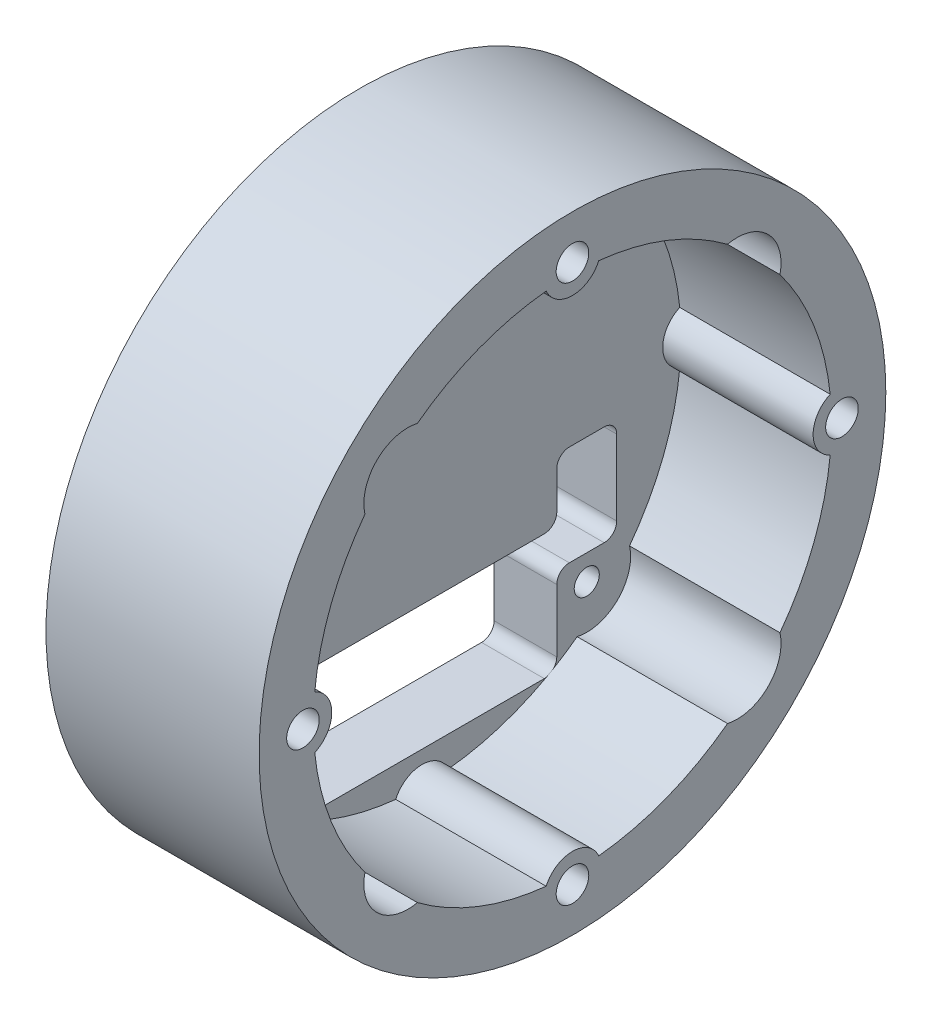
SolidWorks part; units mm, degrees
ref_plane "Front Plane" through (0, 0, 0) normal (0, 0, 1) x (1, 0, 0)
ref_plane "Top Plane" through (0, 0, 0) normal (0, 1, 0) x (1, 0, 0)
ref_plane "Right Plane" through (0, 0, 0) normal (1, 0, 0) x (0, 0, -1)
sketch "Sketch1" plane through (0, 0, 0) normal (1, 0, 0) x (0, 0, -1)
  circle A0 centre (0, 0) radius 25
  dimension "D1" = 50
extrude "Boss-Extrude1" add sketch "Sketch1" along normal blind 5
sketch "Sketch3" plane through (0, 0, 0) normal (-1, 0, 0) x (0, 0, 1)
  circle A0 centre (-13.14, 13.14) radius 1
  circle A1 centre (13.14, 13.14) radius 1
  circle A2 centre (13.14, -13.14) radius 1
  circle A3 centre (-13.14, -13.14) radius 1
  point P12 (0, 0)
  dimension "D1" = 2
  dimension "D2" = 13.14
  dimension "D3" = 13.14
  dimension "D4" = 4
extrude "Cut-Extrude2" cut sketch "Sketch3" against normal through all
sketch "Sketch4" plane through (5, 0, 0) normal (1, 0, 0) x (0, 0, -1)
  circle A0 centre (0, 0) radius 25
  circle A1 centre (0, 0) radius 20.6667
  dimension "D1" = 50
  dimension "D2" = 41.3333
extrude "Boss-Extrude2" add sketch "Sketch4" along normal blind 12
sketch "Sketch2" plane through (5, 0, 0) normal (1, 0, 0) x (0, 0, -1)
  line L0 (0, 21.5) -> (0, 25) construction
  circle A1 centre (0, 21.5) radius 1.3
  circle A3 centre (0, 0) radius 25 construction
  circle A8 centre (21.5, 0) radius 1.3
  circle A9 centre (0, -21.5) radius 1.3
  circle A10 centre (-21.5, 0) radius 1.3
  point P16 (0, 0)
  dimension "D2" = 2.6
  dimension "D1" = 21.5
  dimension "D3" = 4
extrude "Cut-Extrude1" cut sketch "Sketch2" against normal through all both and the other way through all
sketch "Sketch5" plane through (5, 0, 0) normal (1, 0, 0) x (0, 0, -1)
  line L0 (-13.14, -13.14) -> (13.14, -13.14) construction
  line L1 (9.75, -8.14) -> (-9.75, -8.14)
  line L2 (10.75, -12.14) -> (10.75, -17.14)
  line L3 (9.75, -18.14) -> (-9.75, -18.14)
  line L4 (-10.75, -9.14) -> (-10.75, -17.14)
  line L5 (10.75, -8.14) -> (-10.75, -18.14) construction
  line L6 (10.75, -18.14) -> (-10.75, -8.14) construction
  line L8 (14.53, -3.14) -> (11.75, -3.14)
  line L9 (15.53, -4.14) -> (15.53, -10.14)
  line L10 (14.53, -11.14) -> (11.75, -11.14)
  line L11 (10.75, -4.14) -> (10.75, -7.14)
  line L12 (15.53, -3.14) -> (10.75, -11.14) construction
  line L13 (15.53, -11.14) -> (10.75, -3.14) construction
  arc A0 (11.75, -11.14) -> (10.75, -12.14) centre (11.75, -12.14) ccw
  arc A1 (-10.75, -9.14) -> (-9.75, -8.14) centre (-9.75, -9.14) cw
  arc A2 (-9.75, -18.14) -> (-10.75, -17.14) centre (-9.75, -17.14) cw
  arc A3 (10.75, -17.14) -> (9.75, -18.14) centre (9.75, -17.14) cw
  arc A4 (15.53, -10.14) -> (14.53, -11.14) centre (14.53, -10.14) cw
  arc A5 (10.75, -4.14) -> (11.75, -3.14) centre (11.75, -4.14) cw
  arc A6 (15.53, -4.14) -> (14.53, -3.14) centre (14.53, -4.14) ccw
  arc A7 (9.75, -8.14) -> (10.75, -7.14) centre (9.75, -7.14) ccw
  point P0 (0, -13.14)
  point P5 (13.14, -7.14)
  dimension "D5" = 1
  dimension "D6" = 1
  dimension "D1" = 10
  dimension "D2" = 21.5
  dimension "D3" = 8
  dimension "D4" = 2
extrude "Cut-Extrude3" cut sketch "Sketch5" against normal through all
sketch "Sketch7" plane through (5, 0, 0) normal (1, 0, 0) x (0, 0, -1)
  line L0 (-13.14, 13.14) -> (13.14, -13.14) construction
  line L1 (-10.6651, 15.6149) -> (0, 4.9497)
  line L2 (-15.6149, 10.6651) -> (-4.9497, 0)
  line L3 (13.14, 13.14) -> (-13.14, -13.14) construction
  line L4 (15.6149, 10.6651) -> (4.9497, 0)
  line L5 (10.6651, 15.6149) -> (0, 4.9497)
  line L6 (0, -4.9497) -> (10.6651, -15.6149)
  line L7 (0, -4.9497) -> (-10.6651, -15.6149)
  line L8 (4.9497, 0) -> (15.6149, -10.6651)
  line L9 (-4.9497, 0) -> (-15.6149, -10.6651)
  arc A0 (-10.6651, 15.6149) -> (-15.6149, 10.6651) centre (-13.14, 13.14) ccw
  arc A1 (10.6651, -15.6149) -> (15.6149, -10.6651) centre (13.14, -13.14) ccw
  arc A2 (15.6149, 10.6651) -> (10.6651, 15.6149) centre (13.14, 13.14) ccw
  arc A3 (-15.6149, -10.6651) -> (-10.6651, -15.6149) centre (-13.14, -13.14) ccw
  point P2 (0, 0)
  point P11 (0, 0)
extrude "Cut-Extrude5" cut sketch "Sketch7" along normal through all
sketch "Sketch8" plane through (5, 0, 0) normal (1, 0, 0) x (0, 0, -1)
  circle A0 centre (0, -21.5) radius 2.3
  circle A1 centre (0, -21.5) radius 1.3
  circle A2 centre (-21.5, 0) radius 1.3
  circle A3 centre (-21.5, 0) radius 2.3
  circle A4 centre (0, 21.5) radius 1.3
  circle A5 centre (0, 21.5) radius 2.3
  circle A6 centre (21.5, 0) radius 1.3
  circle A7 centre (21.5, 0) radius 2.3
  point P16 (0, 0)
  dimension "D1" = 4.6
  dimension "D2" = 2.6
  dimension "D3" = 4
extrude "Boss-Extrude3" add sketch "Sketch8" along normal up to vertex (12 mm away)
